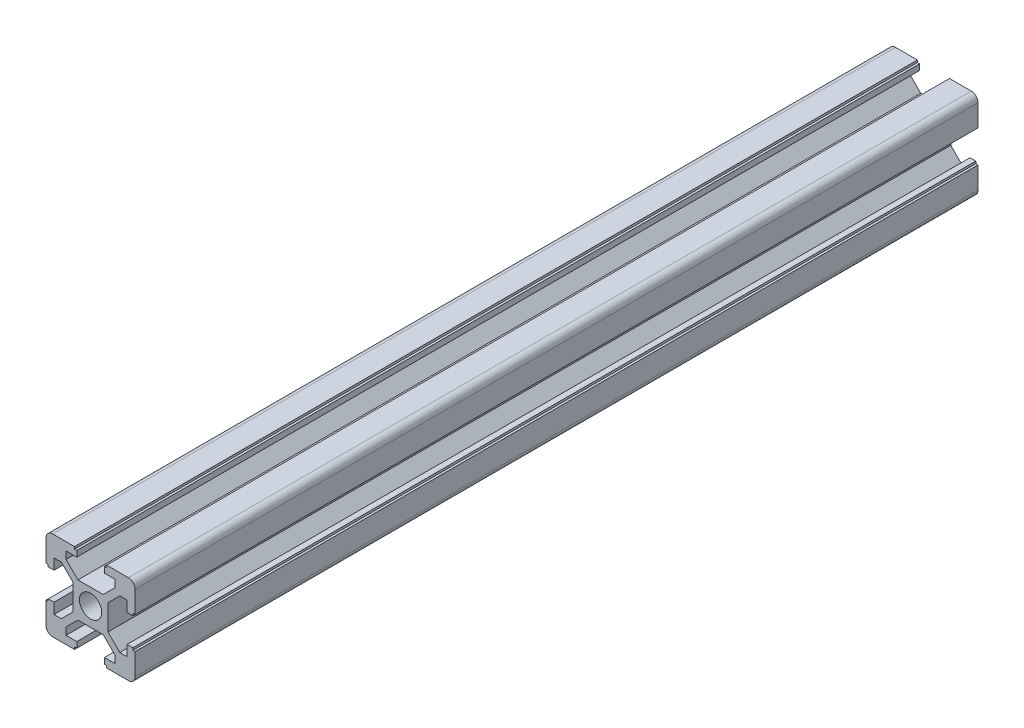
SolidWorks part; units mm, degrees
ref_plane "Front Plane" through (0, 0, 0) normal (0, 0, 1) x (1, 0, 0)
ref_plane "Top Plane" through (0, 0, 0) normal (0, 1, 0) x (1, 0, 0)
ref_plane "Right Plane" through (0, 0, 0) normal (1, 0, 0) x (0, 0, -1)
sketch "Sketch1" plane through (0, 0, 0) normal (0, 0, 1) x (1, 0, 0)
  line L0 (0, 13.3843) -> (0, -12.9126) construction
  line L1 (-14.4653, 0) -> (14.4653, 0) construction
  line L2 (2.8393, 3.9) -> (5.5, 6.5607)
  line L3 (-8.5, 10) -> (-3.6, 10)
  line L4 (-10, 8.5) -> (-10, 3.6)
  line L5 (-8.5, -10) -> (-3.6, -10)
  line L6 (10, 8.5) -> (10, 3.6)
  line L7 (-10, 10) -> (10, -10) construction
  line L8 (-10, -10) -> (10, 10) construction
  line L9 (-5.5, 8.2) -> (-3.1, 8.2)
  line L10 (-5.9626, 4.902) -> (-4.902, 5.9626) construction
  line L11 (-2.8393, 3.9) -> (-5.5, 6.5607)
  line L12 (-5.5, 8.2) -> (-5.5, 6.5607)
  line L13 (-2.8393, 3.9) -> (2.8393, 3.9)
  line L14 (5.5, 8.2) -> (5.5, 6.5607)
  line L15 (-3.1, 9.5) -> (-3.1, 8.2)
  line L16 (3.1, 9.5) -> (3.1, 8.2)
  line L17 (-3.1, 9.5) -> (3.1, 9.5) construction
  line L18 (-3.1, 9.5) -> (-3.6, 9.5)
  line L19 (-3.6, 9.5) -> (-3.6, 10)
  line L20 (3.1, 9.5) -> (3.6, 9.5)
  line L21 (3.6, 9.5) -> (3.6, 10)
  line L22 (3.6, 10) -> (8.5, 10)
  line L23 (3.1, 8.2) -> (5.5, 8.2)
  line L24 (-9.5, -3.1) -> (-9.5, -3.6)
  line L25 (-9.5, -3.6) -> (-10, -3.6)
  line L26 (-9.5, -3.1) -> (-8.2, -3.1)
  line L27 (-8.2, -3.1) -> (-8.2, -5.5)
  line L28 (-8.2, -5.5) -> (-6.5607, -5.5)
  line L29 (-3.9, -2.8393) -> (-6.5607, -5.5)
  line L30 (-3.9, 2.8393) -> (-3.9, -2.8393)
  line L31 (-3.9, 2.8393) -> (-6.5607, 5.5)
  line L32 (-8.2, 5.5) -> (-6.5607, 5.5)
  line L33 (-8.2, 5.5) -> (-8.2, 3.1)
  line L34 (-9.5, 3.1) -> (-8.2, 3.1)
  line L35 (-9.5, 3.1) -> (-9.5, 3.6)
  line L36 (-9.5, 3.6) -> (-10, 3.6)
  line L37 (-3.6, -9.5) -> (-3.6, -10)
  line L38 (-3.1, -9.5) -> (-3.6, -9.5)
  line L39 (-3.1, -9.5) -> (-3.1, -8.2)
  line L40 (-3.1, -8.2) -> (-5.5, -8.2)
  line L41 (-5.5, -8.2) -> (-5.5, -6.5607)
  line L42 (-2.8393, -3.9) -> (-5.5, -6.5607)
  line L43 (2.8393, -3.9) -> (-2.8393, -3.9)
  line L44 (2.8393, -3.9) -> (5.5, -6.5607)
  line L45 (5.5, -8.2) -> (5.5, -6.5607)
  line L46 (5.5, -8.2) -> (3.1, -8.2)
  line L47 (3.1, -9.5) -> (3.6, -9.5)
  line L48 (3.1, -9.5) -> (3.1, -8.2)
  line L49 (3.6, -9.5) -> (3.6, -10)
  line L50 (9.5, -3.6) -> (10, -3.6)
  line L51 (9.5, -3.1) -> (9.5, -3.6)
  line L52 (9.5, -3.1) -> (8.2, -3.1)
  line L53 (8.2, -5.5) -> (8.2, -3.1)
  line L54 (8.2, -5.5) -> (6.5607, -5.5)
  line L55 (3.9, -2.8393) -> (6.5607, -5.5)
  line L56 (3.9, -2.8393) -> (3.9, 2.8393)
  line L57 (3.9, 2.8393) -> (6.5607, 5.5)
  line L58 (8.2, 5.5) -> (6.5607, 5.5)
  line L59 (8.2, 3.1) -> (8.2, 5.5)
  line L60 (9.5, 3.1) -> (8.2, 3.1)
  line L61 (9.5, 3.1) -> (9.5, 3.6)
  line L62 (9.5, 3.6) -> (10, 3.6)
  line L63 (-10, -3.6) -> (-10, -8.5)
  line L64 (3.6, -10) -> (8.5, -10)
  line L65 (10, -3.6) -> (10, -8.5)
  arc A0 (8.5, 10) -> (10, 8.5) centre (8.5, 8.5) cw
  arc A1 (8.5, -10) -> (10, -8.5) centre (8.5, -8.5) ccw
  arc A2 (-10, -8.5) -> (-8.5, -10) centre (-8.5, -8.5) ccw
  arc A3 (-8.5, 10) -> (-10, 8.5) centre (-8.5, 8.5) ccw
  circle A4 centre (0, 0.2358) radius 2.5
  point P5 (0, 0)
  point P30 (-5.4323, 5.4323)
  point P38 (0, 9.5)
  dimension "D3" = 1.5
  dimension "D15" = 5
  dimension "D1" = 20
  dimension "D2" = 20
  dimension "D4" = 6.2
  dimension "D5" = 11
  dimension "D6" = 1.8
  dimension "D7" = 1.5
  dimension "D8" = 90
  dimension "D9" = 0.5
  dimension "D10" = 0.5
  dimension "D11" = 0.5
  dimension "D12" = 0.5
  dimension "D13" = 6.1
  dimension "D14" = 45
extrude "Boss-Extrude1" add sketch "Sketch1" along normal blind 189.0961
scale "缩放比例1" bodies to scale 101 scale about centroid uniform scaling yes scale factor 1
scale "缩放比例2" scale about centroid uniform scaling yes scale factor 3
scale "缩放比例3" scale about centroid uniform scaling yes scale factor 6
scale "缩放比例5" scale about centroid uniform scaling yes scale factor 2
scale "缩放比例6" scale about centroid uniform scaling yes scale factor 0.25
scale "缩放比例7" scale about centroid uniform scaling yes scale factor 0.125
scale "缩放比例8" scale about centroid uniform scaling yes scale factor 0.25
scale "缩放比例9" scale about centroid uniform scaling yes scale factor 4
scale "缩放比例10" scale about centroid uniform scaling yes scale factor 4
scale "缩放比例11" scale about centroid uniform scaling yes scale factor 0.111111
